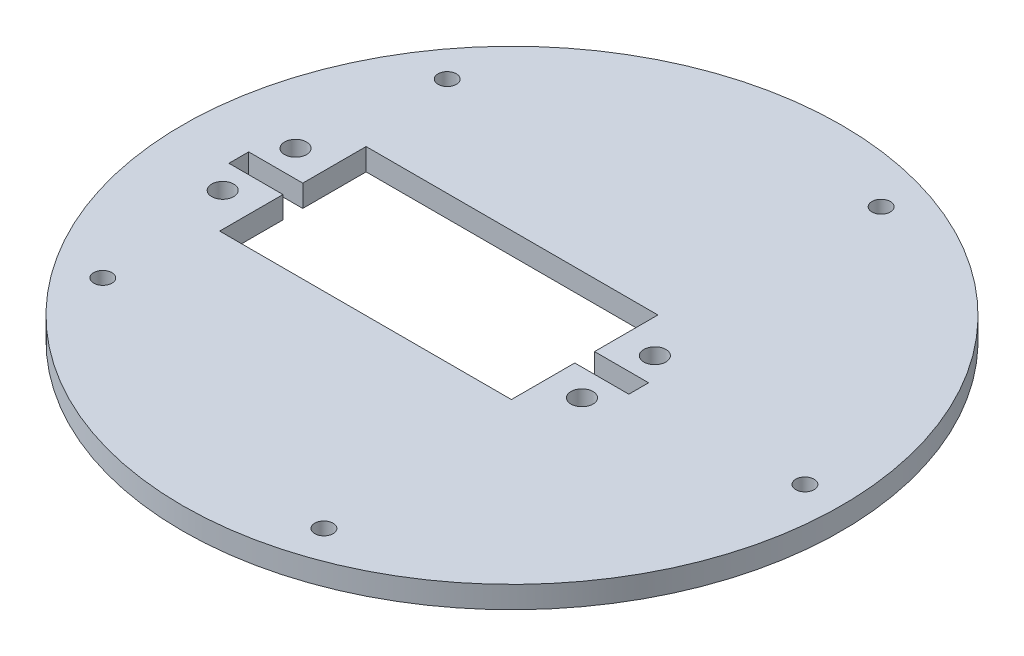
SolidWorks part; units mm, degrees
ref_plane "前视基准面" through (0, 0, 0) normal (0, 0, 1) x (1, 0, 0)
ref_plane "上视基准面" through (0, 0, 0) normal (0, 1, 0) x (1, 0, 0)
ref_plane "右视基准面" through (0, 0, 0) normal (1, 0, 0) x (0, 0, -1)
other "Configuration Table"
sketch "草图1" plane through (0, 0, 0) normal (0, 1, 0) x (1, 0, 0)
  line L0 (0, 0) -> (59.4554, 0) construction
  circle A0 centre (0, 0) radius 45
  point P3 (40, 0)
  point P6 (45, 0)
  dimension "D1" = 90
  dimension "D2" = 5
extrude "凸台-拉伸1" add sketch "草图1" along normal blind 3 contours A0
sketch "草图2" plane through (0, 0, 0) normal (0, 1, 0) x (1, 0, 0)
  line L0 (0, 0) -> (63.3795, 0) construction
  circle A0 centre (0, 0) radius 45 construction
  point P0 (40, 0)
  point P6 (12.3607, -38.0423)
  point P7 (-32.3607, -23.5114)
  point P8 (-32.3607, 23.5114)
  point P9 (12.3607, 38.0423)
  point P10 (0, 0)
  dimension "D1" = 40
  dimension "D2" = 5
hole_wizard "M3 螺纹孔的螺纹孔钻头1" positions "草图2" profile "草图3" hole size "M3" standard "GB"
sketch "草图3" plane through (40, 0, 0) normal (1, 0, 0) x (0, 0, -1)
  line L0 (0, 0) -> (0, 3)
  line L1 (0, 3) -> (1.25, 3)
  line L2 (1.25, 3) -> (1.25, 0.025)
  line L3 (1.25, 0.025) -> (1.275, 0)
  line L5 (1.275, 0) -> (0, 0)
  line L6 (-1.25, 0.025) -> (-1.275, 0) construction
  line L11 (0, -6.35) -> (0, 107.95) construction
  dimension "通孔孔直径" = 2.5
  dimension "通孔孔深度" = 3
  dimension "近端锥形沉头孔直径" = 2.55
  dimension "近端锥形沉头孔角度" = 90
cosmetic thread "装饰螺纹线1" parameters "D2"=3
cosmetic thread "装饰螺纹线2" parameters "D2"=3
cosmetic thread "装饰螺纹线3" parameters "D2"=3
cosmetic thread "装饰螺纹线4" parameters "D2"=3
cosmetic thread "装饰螺纹线5" parameters "D2"=3
sketch "草图4" plane through (0, 3, 0) normal (0, 1, 0) x (1, 0, 0)
  line L0 (-9.1841, 13.2038) -> (45.4259, 28.2038) construction
  line L1 (-9.1841, 28.2038) -> (45.4259, 28.2038) construction
  line L2 (-9.1841, 28.2038) -> (-9.1841, 13.2038) construction
  line L3 (-9.1841, 13.2038) -> (45.4259, 13.2038) construction
  line L4 (45.4259, 28.2038) -> (45.4259, 13.2038) construction
  line L5 (-1.7991, 25.6788) -> (38.0409, 25.6788) construction
  line L6 (-1.7991, 25.6788) -> (-1.7991, 15.7288) construction
  line L7 (-1.7991, 15.7288) -> (38.0409, 15.7288) construction
  line L8 (38.0409, 25.6788) -> (38.0409, 15.7288) construction
  line L9 (-9.1841, 28.2038) -> (45.4259, 13.2038) construction
  line L10 (38.0409, 25.6788) -> (-1.7991, 15.7288) construction
  line L11 (-1.7991, 25.6788) -> (38.0409, 15.7288) construction
  line L12 (28.1209, 25.6788) -> (28.1209, 15.7288) construction
  line L13 (-9.1841, 20.7038) -> (45.4259, 20.7038) construction
  line L14 (-6.4091, 25.6788) -> (42.6509, 25.6788) construction
  line L15 (-6.4091, 25.6788) -> (-6.4091, 15.7288) construction
  line L16 (-6.4091, 15.7288) -> (42.6509, 15.7288) construction
  line L17 (42.6509, 25.6788) -> (42.6509, 15.7288) construction
  line L18 (-6.4091, 25.6788) -> (42.6509, 15.7288) construction
  line L19 (-6.4091, 15.7288) -> (42.6509, 25.6788) construction
  line L20 (18.1209, 28.2038) -> (18.1209, 13.2038) construction
  line L21 (-1.7991, 19.3538) -> (-9.1841, 22.0538) construction
  line L22 (38.0409, 22.0538) -> (45.4259, 22.0538)
  line L23 (38.0409, 22.0538) -> (38.0409, 19.3538)
  line L24 (38.0409, 19.3538) -> (45.4259, 19.3538)
  line L25 (45.4259, 22.0538) -> (45.4259, 19.3538)
  line L26 (38.0409, 22.0538) -> (45.4259, 19.3538) construction
  line L27 (38.0409, 19.3538) -> (45.4259, 22.0538) construction
  line L28 (-1.7991, 22.0538) -> (-9.1841, 19.3538) construction
  line L29 (-9.1841, 22.0538) -> (-9.1841, 19.3538)
  line L30 (-1.7991, 19.3538) -> (-9.1841, 19.3538)
  line L31 (-1.7991, 22.0538) -> (-1.7991, 19.3538)
  line L32 (-1.7991, 22.0538) -> (-9.1841, 22.0538)
  line L34 (-1.7991, 30.7038) -> (38.0409, 30.7038)
  line L35 (-1.7991, 30.7038) -> (-1.7991, 10.7038)
  line L36 (-1.7991, 10.7038) -> (38.0409, 10.7038)
  line L37 (38.0409, 30.7038) -> (38.0409, 10.7038)
  line L38 (-1.7991, 30.7038) -> (38.0409, 10.7038) construction
  line L39 (-1.7991, 10.7038) -> (38.0409, 30.7038) construction
  circle A0 centre (28.1209, 20.7038) radius 2.5
  circle A1 centre (42.6509, 25.6788) radius 2
  circle A2 centre (42.6509, 15.7288) radius 2
  circle A3 centre (-6.4091, 25.6788) radius 2
  circle A4 centre (-6.4091, 15.7288) radius 2
  point P4 (18.1209, 20.7038)
  point P9 (18.1209, 20.7038)
  point P10 (18.1209, 20.7038)
  point P27 (38.0409, 20.7038)
  point P28 (41.7334, 20.7038)
  point P37 (-5.4916, 20.7038)
  point P38 (-1.7991, 20.7038)
  point P39 (18.1209, 20.7038)
  point P47 (28.1209, 20.7038)
  dimension "D7" = 5
  dimension "D8" = 4
  dimension "D9" = 4
  dimension "D10" = 4
  dimension "D11" = 4
  dimension "D1" = 54.61
  dimension "D2" = 15
  dimension "D3" = 9.95
  dimension "D4" = 39.84
  dimension "D5" = 29.92
  dimension "D6" = 49.06
  dimension "D12" = 2.7
  dimension "D13" = 20
sketch "草图7" plane through (0, 0, 0) normal (0, 1, 0) x (1, 0, 0)
  line L0 (-37.305, -7.5) -> (17.305, 7.5) construction
  line L1 (-37.305, 7.5) -> (17.305, 7.5) construction
  line L2 (-37.305, 7.5) -> (-37.305, -7.5) construction
  line L3 (-37.305, -7.5) -> (17.305, -7.5) construction
  line L4 (17.305, 7.5) -> (17.305, -7.5) construction
  line L5 (-29.92, 4.975) -> (9.92, 4.975) construction
  line L6 (-29.92, 4.975) -> (-29.92, -4.975) construction
  line L7 (-29.92, -4.975) -> (9.92, -4.975) construction
  line L8 (9.92, 4.975) -> (9.92, -4.975) construction
  line L9 (-37.305, 7.5) -> (17.305, -7.5) construction
  line L10 (9.92, 4.975) -> (-29.92, -4.975) construction
  line L11 (-29.92, 4.975) -> (9.92, -4.975) construction
  line L12 (0, 4.975) -> (0, -4.975) construction
  line L13 (-37.305, 0) -> (17.305, 0) construction
  line L14 (-34.53, 4.975) -> (14.53, 4.975) construction
  line L15 (-34.53, 4.975) -> (-34.53, -4.975) construction
  line L16 (-34.53, -4.975) -> (14.53, -4.975) construction
  line L17 (14.53, 4.975) -> (14.53, -4.975) construction
  line L18 (-34.53, 4.975) -> (14.53, -4.975) construction
  line L19 (-34.53, -4.975) -> (14.53, 4.975) construction
  line L20 (-10, 7.5) -> (-10, -7.5) construction
  line L21 (-29.92, -1.35) -> (-37.305, 1.35) construction
  line L22 (9.92, 1.35) -> (17.305, 1.35)
  line L23 (9.92, 1.35) -> (9.92, -1.35)
  line L24 (9.92, -1.35) -> (17.305, -1.35)
  line L25 (17.305, 1.35) -> (17.305, -1.35)
  line L26 (9.92, 1.35) -> (17.305, -1.35) construction
  line L27 (9.92, -1.35) -> (17.305, 1.35) construction
  line L28 (-29.92, 1.35) -> (-37.305, -1.35) construction
  line L29 (-37.305, 1.35) -> (-37.305, -1.35)
  line L30 (-29.92, -1.35) -> (-37.305, -1.35)
  line L31 (-29.92, 1.35) -> (-29.92, -1.35)
  line L32 (-29.92, 1.35) -> (-37.305, 1.35)
  line L34 (-29.92, 10) -> (9.92, 10)
  line L35 (-29.92, 10) -> (-29.92, -10)
  line L36 (-29.92, -10) -> (9.92, -10)
  line L37 (9.92, 10) -> (9.92, -10)
  line L38 (-29.92, 10) -> (9.92, -10) construction
  line L39 (-29.92, -10) -> (9.92, 10) construction
  circle A0 centre (0, 0) radius 2.5
  circle A1 centre (14.53, 4.975) radius 1.5
  circle A2 centre (14.53, -4.975) radius 1.5
  circle A3 centre (-34.53, 4.975) radius 1.5
  circle A4 centre (-34.53, -4.975) radius 1.5
  point P4 (-10, 0)
  point P9 (-10, 0)
  point P10 (-10, 0)
  point P27 (9.92, 0)
  point P28 (13.6125, 0)
  point P37 (-33.6125, 0)
  point P38 (-29.92, 0)
  point P39 (-10, 0)
  point P49 (0, 0)
  dimension "D7" = 5
  dimension "D8" = 3
  dimension "D9" = 3
  dimension "D10" = 3
  dimension "D11" = 3
  dimension "D1" = 54.61
  dimension "D2" = 15
  dimension "D3" = 9.95
  dimension "D4" = 39.84
  dimension "D5" = 29.92
  dimension "D6" = 49.06
  dimension "D12" = 2.7
  dimension "D13" = 20
extrude "切除-拉伸1" cut sketch "草图7" against normal through all both and the other way through all contours L36 L37 L34 L35 | A4 | A3 | A1 | A2 | L24 L25 L22 L23 | L30 L29 L32 L31
